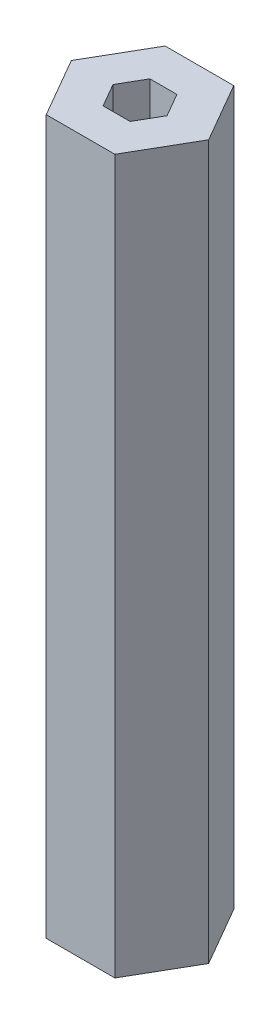
SolidWorks part; units mm, degrees
material "6061-T6 (SS)"
ref_plane "Front" through (0, 0, 0) normal (0, 0, 1) x (1, 0, 0)
ref_plane "Top" through (0, 0, 0) normal (0, 1, 0) x (1, 0, 0)
ref_plane "Right" through (0, 0, 0) normal (1, 0, 0) x (0, 0, -1)
sketch "Sketch1" plane through (0, 0, 0) normal (0, 1, 0) x (1, 0, 0)
  line L1 (7.3323, 0) -> (3.6662, 6.35)
  line L2 (3.6662, 6.35) -> (-3.6662, 6.35)
  line L3 (-3.6662, 6.35) -> (-7.3323, 0)
  line L4 (-7.3323, 0) -> (-3.6662, -6.35)
  line L5 (-3.6662, -6.35) -> (3.6662, -6.35)
  line L6 (3.6662, -6.35) -> (7.3323, 0)
  line L7 (2.8868, 0) -> (1.4434, 2.5)
  line L8 (1.4434, 2.5) -> (-1.4434, 2.5)
  line L9 (-1.4434, 2.5) -> (-2.8868, 0)
  line L10 (-2.8868, 0) -> (-1.4434, -2.5)
  line L11 (-1.4434, -2.5) -> (1.4434, -2.5)
  line L12 (1.4434, -2.5) -> (2.8868, 0)
  circle A0 centre (0, 0) radius 6.35 construction
  circle A1 centre (0, 0) radius 2.5 construction
  dimension "D1" = 12.7
  dimension "D2" = 5
extrude "Boss-Extrude1" add sketch "Sketch1" along normal blind 76.2
